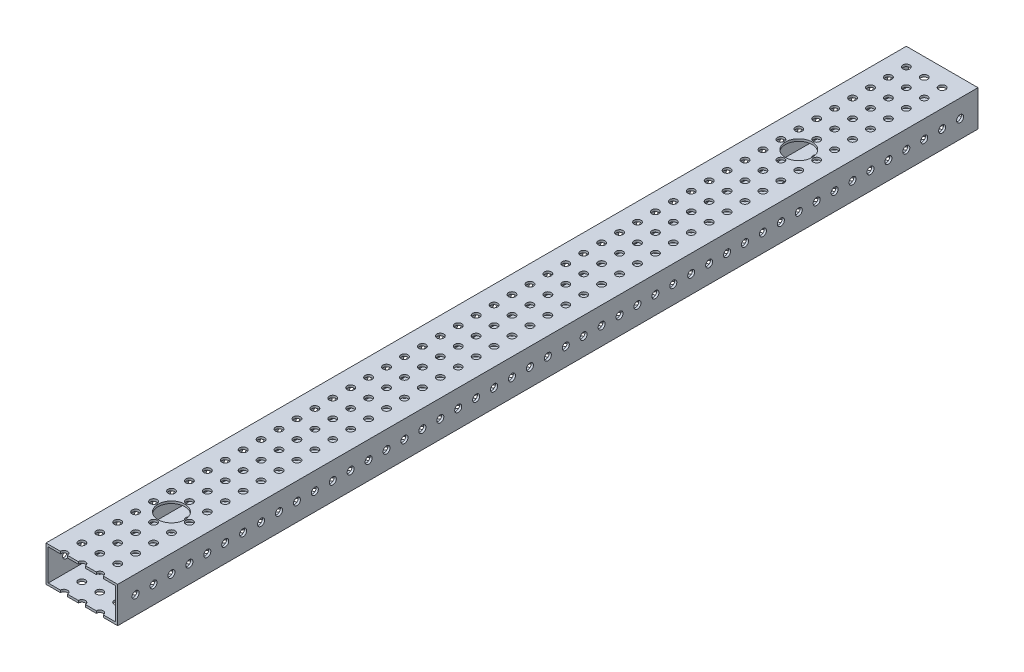
SolidWorks part; units mm, degrees
material "6061 Alloy"
ref_plane "Front Plane" through (0, 0, 0) normal (0, 0, 1) x (1, 0, 0)
ref_plane "Top Plane" through (0, 0, 0) normal (0, 1, 0) x (1, 0, 0)
ref_plane "Right Plane" through (0, 0, 0) normal (1, 0, 0) x (0, 0, -1)
sketch "Sketch1" plane through (0, 0, 0) normal (0, 0, 1) x (1, 0, 0)
  line L0 (1.5875, 1.5875) -> (49.2125, 1.5875)
  line L1 (0, 0) -> (50.8, 0)
  line L2 (0, 0) -> (0, 25.4)
  line L3 (0, 25.4) -> (50.8, 25.4)
  line L4 (50.8, 0) -> (50.8, 25.4)
  line L5 (49.2125, 1.5875) -> (49.2125, 23.8125)
  line L6 (1.5875, 23.8125) -> (49.2125, 23.8125)
  line L7 (1.5875, 1.5875) -> (1.5875, 23.8125)
  dimension "D1" = 50.8
  dimension "D2" = 25.4
  dimension "D3" = 1.5875
extrude "Boss-Extrude1" add sketch "Sketch1" along normal blind 609.6
sketch "Sketch2" plane through (50.8, 0, 0) normal (1, 0, 0) x (0, 0, -1)
  line L0 (-609.6, 0) -> (-609.6, 25.4) construction
  line L1 (-596.9, 12.7) -> (-584.2, 12.7) construction
  circle A0 centre (-596.9, 12.7) radius 2.4892
  circle A1 centre (-584.2, 12.7) radius 2.4892
  circle A2 centre (-571.5, 12.7) radius 2.4892
  circle A3 centre (-558.8, 12.7) radius 2.4892
  circle A4 centre (-546.1, 12.7) radius 2.4892
  circle A5 centre (-533.4, 12.7) radius 2.4892
  circle A6 centre (-520.7, 12.7) radius 2.4892
  circle A7 centre (-508, 12.7) radius 2.4892
  circle A8 centre (-495.3, 12.7) radius 2.4892
  circle A9 centre (-482.6, 12.7) radius 2.4892
  circle A10 centre (-469.9, 12.7) radius 2.4892
  circle A11 centre (-457.2, 12.7) radius 2.4892
  circle A12 centre (-444.5, 12.7) radius 2.4892
  circle A13 centre (-431.8, 12.7) radius 2.4892
  circle A14 centre (-419.1, 12.7) radius 2.4892
  circle A15 centre (-406.4, 12.7) radius 2.4892
  circle A16 centre (-393.7, 12.7) radius 2.4892
  circle A17 centre (-381, 12.7) radius 2.4892
  circle A18 centre (-368.3, 12.7) radius 2.4892
  circle A19 centre (-355.6, 12.7) radius 2.4892
  circle A20 centre (-342.9, 12.7) radius 2.4892
  circle A21 centre (-330.2, 12.7) radius 2.4892
  circle A22 centre (-317.5, 12.7) radius 2.4892
  circle A23 centre (-304.8, 12.7) radius 2.4892
  circle A24 centre (-292.1, 12.7) radius 2.4892
  circle A25 centre (-279.4, 12.7) radius 2.4892
  circle A26 centre (-266.7, 12.7) radius 2.4892
  circle A27 centre (-254, 12.7) radius 2.4892
  circle A28 centre (-241.3, 12.7) radius 2.4892
  circle A29 centre (-228.6, 12.7) radius 2.4892
  circle A30 centre (-215.9, 12.7) radius 2.4892
  circle A31 centre (-203.2, 12.7) radius 2.4892
  circle A32 centre (-190.5, 12.7) radius 2.4892
  circle A33 centre (-177.8, 12.7) radius 2.4892
  circle A34 centre (-165.1, 12.7) radius 2.4892
  circle A35 centre (-152.4, 12.7) radius 2.4892
  circle A36 centre (-139.7, 12.7) radius 2.4892
  circle A37 centre (-127, 12.7) radius 2.4892
  circle A38 centre (-114.3, 12.7) radius 2.4892
  circle A39 centre (-101.6, 12.7) radius 2.4892
  circle A40 centre (-88.9, 12.7) radius 2.4892
  circle A41 centre (-76.2, 12.7) radius 2.4892
  circle A42 centre (-63.5, 12.7) radius 2.4892
  circle A43 centre (-50.8, 12.7) radius 2.4892
  circle A44 centre (-38.1, 12.7) radius 2.4892
  circle A45 centre (-25.4, 12.7) radius 2.4892
  circle A46 centre (-12.7, 12.7) radius 2.4892
  point P4 (-609.6, 12.7)
  dimension "D1" = 4.9784
  dimension "D2" = 12.7
  dimension "D4" = 12.7
  dimension "D3" = 47
extrude "Cut-Extrude1" cut sketch "Sketch2" against normal through all
sketch "Sketch4" plane through (0, 25.4, 0) normal (0, 1, 0) x (1, 0, 0)
  line L0 (50.8, 0) -> (0, 0) construction
  line L1 (0, -609.6) -> (0, 0) construction
  line L2 (12.7, -12.7) -> (25.4, -12.7) construction
  line L3 (12.7, -12.7) -> (12.7, -25.4) construction
  circle A0 centre (12.7, -12.7) radius 2.4892
  circle A1 centre (25.4, -12.7) radius 2.4892
  circle A2 centre (38.1, -12.7) radius 2.4892
  circle A3 centre (25.4, -25.4) radius 2.4892
  circle A4 centre (38.1, -25.4) radius 2.4892
  circle A5 centre (25.4, -38.1) radius 2.4892
  circle A6 centre (38.1, -38.1) radius 2.4892
  circle A7 centre (25.4, -50.8) radius 2.4892
  circle A8 centre (38.1, -50.8) radius 2.4892
  circle A9 centre (25.4, -63.5) radius 2.4892
  circle A10 centre (38.1, -63.5) radius 2.4892
  circle A11 centre (25.4, -76.2) radius 2.4892
  circle A12 centre (38.1, -76.2) radius 2.4892
  circle A13 centre (25.4, -88.9) radius 2.4892
  circle A14 centre (38.1, -88.9) radius 2.4892
  circle A15 centre (25.4, -101.6) radius 2.4892
  circle A16 centre (38.1, -101.6) radius 2.4892
  circle A17 centre (25.4, -114.3) radius 2.4892
  circle A18 centre (38.1, -114.3) radius 2.4892
  circle A19 centre (25.4, -127) radius 2.4892
  circle A20 centre (38.1, -127) radius 2.4892
  circle A21 centre (25.4, -139.7) radius 2.4892
  circle A22 centre (38.1, -139.7) radius 2.4892
  circle A23 centre (25.4, -152.4) radius 2.4892
  circle A24 centre (38.1, -152.4) radius 2.4892
  circle A25 centre (25.4, -165.1) radius 2.4892
  circle A26 centre (38.1, -165.1) radius 2.4892
  circle A27 centre (25.4, -177.8) radius 2.4892
  circle A28 centre (38.1, -177.8) radius 2.4892
  circle A29 centre (25.4, -190.5) radius 2.4892
  circle A30 centre (38.1, -190.5) radius 2.4892
  circle A31 centre (25.4, -203.2) radius 2.4892
  circle A32 centre (38.1, -203.2) radius 2.4892
  circle A33 centre (25.4, -215.9) radius 2.4892
  circle A34 centre (38.1, -215.9) radius 2.4892
  circle A35 centre (25.4, -228.6) radius 2.4892
  circle A36 centre (38.1, -228.6) radius 2.4892
  circle A37 centre (25.4, -241.3) radius 2.4892
  circle A38 centre (38.1, -241.3) radius 2.4892
  circle A39 centre (25.4, -254) radius 2.4892
  circle A40 centre (38.1, -254) radius 2.4892
  circle A41 centre (25.4, -266.7) radius 2.4892
  circle A42 centre (38.1, -266.7) radius 2.4892
  circle A43 centre (25.4, -279.4) radius 2.4892
  circle A44 centre (38.1, -279.4) radius 2.4892
  circle A45 centre (25.4, -292.1) radius 2.4892
  circle A46 centre (38.1, -292.1) radius 2.4892
  circle A47 centre (25.4, -304.8) radius 2.4892
  circle A48 centre (38.1, -304.8) radius 2.4892
  circle A49 centre (25.4, -317.5) radius 2.4892
  circle A50 centre (38.1, -317.5) radius 2.4892
  circle A51 centre (25.4, -330.2) radius 2.4892
  circle A52 centre (38.1, -330.2) radius 2.4892
  circle A53 centre (25.4, -342.9) radius 2.4892
  circle A54 centre (38.1, -342.9) radius 2.4892
  circle A55 centre (25.4, -355.6) radius 2.4892
  circle A56 centre (38.1, -355.6) radius 2.4892
  circle A57 centre (25.4, -368.3) radius 2.4892
  circle A58 centre (38.1, -368.3) radius 2.4892
  circle A59 centre (25.4, -381) radius 2.4892
  circle A60 centre (38.1, -381) radius 2.4892
  circle A61 centre (25.4, -393.7) radius 2.4892
  circle A62 centre (38.1, -393.7) radius 2.4892
  circle A63 centre (25.4, -406.4) radius 2.4892
  circle A64 centre (38.1, -406.4) radius 2.4892
  circle A65 centre (25.4, -419.1) radius 2.4892
  circle A66 centre (38.1, -419.1) radius 2.4892
  circle A67 centre (25.4, -431.8) radius 2.4892
  circle A68 centre (38.1, -431.8) radius 2.4892
  circle A69 centre (25.4, -444.5) radius 2.4892
  circle A70 centre (38.1, -444.5) radius 2.4892
  circle A71 centre (25.4, -457.2) radius 2.4892
  circle A72 centre (38.1, -457.2) radius 2.4892
  circle A73 centre (25.4, -469.9) radius 2.4892
  circle A74 centre (38.1, -469.9) radius 2.4892
  circle A75 centre (25.4, -482.6) radius 2.4892
  circle A76 centre (38.1, -482.6) radius 2.4892
  circle A77 centre (25.4, -495.3) radius 2.4892
  circle A78 centre (38.1, -495.3) radius 2.4892
  circle A79 centre (25.4, -508) radius 2.4892
  circle A80 centre (38.1, -508) radius 2.4892
  circle A81 centre (25.4, -520.7) radius 2.4892
  circle A82 centre (38.1, -520.7) radius 2.4892
  circle A83 centre (25.4, -533.4) radius 2.4892
  circle A84 centre (38.1, -533.4) radius 2.4892
  circle A85 centre (25.4, -546.1) radius 2.4892
  circle A86 centre (38.1, -546.1) radius 2.4892
  circle A87 centre (25.4, -558.8) radius 2.4892
  circle A88 centre (38.1, -558.8) radius 2.4892
  circle A89 centre (25.4, -571.5) radius 2.4892
  circle A90 centre (38.1, -571.5) radius 2.4892
  circle A91 centre (25.4, -584.2) radius 2.4892
  circle A92 centre (38.1, -584.2) radius 2.4892
  circle A93 centre (25.4, -596.9) radius 2.4892
  circle A94 centre (38.1, -596.9) radius 2.4892
  circle A95 centre (25.4, -609.6) radius 2.4892
  circle A96 centre (38.1, -609.6) radius 2.4892
  circle A97 centre (12.7, -25.4) radius 2.4892
  circle A98 centre (12.7, -38.1) radius 2.4892
  circle A99 centre (12.7, -50.8) radius 2.4892
  circle A100 centre (12.7, -63.5) radius 2.4892
  circle A101 centre (12.7, -76.2) radius 2.4892
  circle A102 centre (12.7, -88.9) radius 2.4892
  circle A103 centre (12.7, -101.6) radius 2.4892
  circle A104 centre (12.7, -114.3) radius 2.4892
  circle A105 centre (12.7, -127) radius 2.4892
  circle A106 centre (12.7, -139.7) radius 2.4892
  circle A107 centre (12.7, -152.4) radius 2.4892
  circle A108 centre (12.7, -165.1) radius 2.4892
  circle A109 centre (12.7, -177.8) radius 2.4892
  circle A110 centre (12.7, -190.5) radius 2.4892
  circle A111 centre (12.7, -203.2) radius 2.4892
  circle A112 centre (12.7, -215.9) radius 2.4892
  circle A113 centre (12.7, -228.6) radius 2.4892
  circle A114 centre (12.7, -241.3) radius 2.4892
  circle A115 centre (12.7, -254) radius 2.4892
  circle A116 centre (12.7, -266.7) radius 2.4892
  circle A117 centre (12.7, -279.4) radius 2.4892
  circle A118 centre (12.7, -292.1) radius 2.4892
  circle A119 centre (12.7, -304.8) radius 2.4892
  circle A120 centre (12.7, -317.5) radius 2.4892
  circle A121 centre (12.7, -330.2) radius 2.4892
  circle A122 centre (12.7, -342.9) radius 2.4892
  circle A123 centre (12.7, -355.6) radius 2.4892
  circle A124 centre (12.7, -368.3) radius 2.4892
  circle A125 centre (12.7, -381) radius 2.4892
  circle A126 centre (12.7, -393.7) radius 2.4892
  circle A127 centre (12.7, -406.4) radius 2.4892
  circle A128 centre (12.7, -419.1) radius 2.4892
  circle A129 centre (12.7, -431.8) radius 2.4892
  circle A130 centre (12.7, -444.5) radius 2.4892
  circle A131 centre (12.7, -457.2) radius 2.4892
  circle A132 centre (12.7, -469.9) radius 2.4892
  circle A133 centre (12.7, -482.6) radius 2.4892
  circle A134 centre (12.7, -495.3) radius 2.4892
  circle A135 centre (12.7, -508) radius 2.4892
  circle A136 centre (12.7, -520.7) radius 2.4892
  circle A137 centre (12.7, -533.4) radius 2.4892
  circle A138 centre (12.7, -546.1) radius 2.4892
  circle A139 centre (12.7, -558.8) radius 2.4892
  circle A140 centre (12.7, -571.5) radius 2.4892
  circle A141 centre (12.7, -584.2) radius 2.4892
  circle A142 centre (12.7, -596.9) radius 2.4892
  circle A143 centre (12.7, -609.6) radius 2.4892
  dimension "D1" = 4.9784
  dimension "D2" = 12.7
  dimension "D3" = 12.7
  dimension "D6" = 90
  dimension "D7" = 12.7
  dimension "D8" = 12.7
  dimension "D4" = 3
  dimension "D5" = 48
extrude "Cut-Extrude3" cut sketch "Sketch4" against normal through all
sketch "Sketch3" plane through (0, 0, 0) normal (0, -1, 0) x (1, 0, 0)
  line L0 (0, 609.6) -> (0, 0) construction
  line L2 (0, 304.8) -> (50.8, 304.8) construction
  line L3 (50.8, 609.6) -> (50.8, 0) construction
  circle A0 centre (25.4, 546.1) radius 9.525
  circle A1 centre (25.4, 101.6) radius 9.525
  point P2 (92.635, 520.1619)
  point P6 (25.4, 546.1)
  point P7 (0, 0)
  point P14 (25.4, 76.2)
  point P16 (0, 0)
  point P17 (25.4, 533.4)
  point P19 (0, 0)
  point P20 (25.4, 546.1)
  point P22 (0, 0)
  point P23 (25.4, 101.6)
  dimension "D1" = 19.05
extrude "Cut-Extrude2" cut sketch "Sketch3" against normal through all
